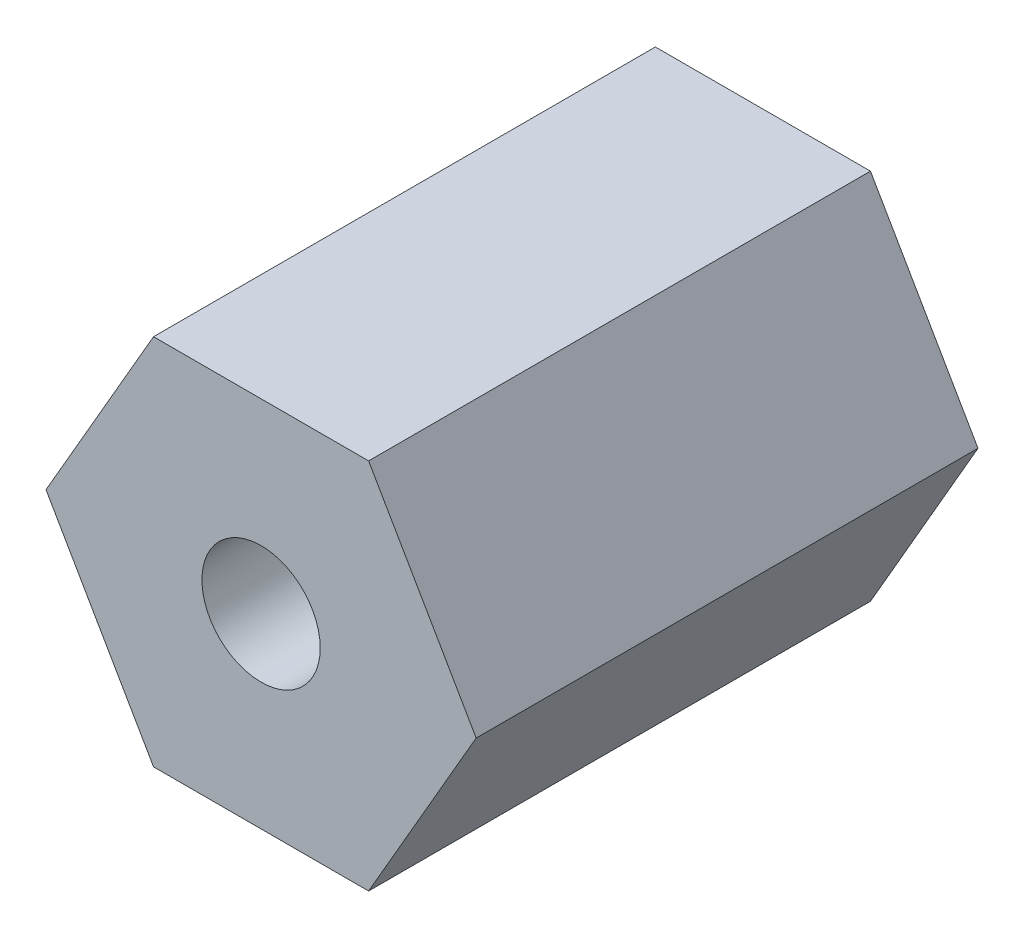
SolidWorks part; units mm, degrees
material "1060 合金"
ref_plane "前视基准面" through (0, 0, 0) normal (0, 0, 1) x (1, 0, 0)
ref_plane "上视基准面" through (0, 0, 0) normal (0, 1, 0) x (1, 0, 0)
ref_plane "右视基准面" through (0, 0, 0) normal (1, 0, 0) x (0, 0, -1)
other "Configuration Table"
sketch "草图1" plane through (0, 0, 0) normal (0, 0, 1) x (1, 0, 0)
  line L1 (-3, 5.1962) -> (-6, 0)
  line L2 (-6, 0) -> (-3, -5.1962)
  line L3 (-3, -5.1962) -> (3, -5.1962)
  line L4 (3, -5.1962) -> (6, 0)
  line L5 (6, 0) -> (3, 5.1962)
  line L6 (3, 5.1962) -> (-3, 5.1962)
  circle A0 centre (0, 0) radius 5.1962 construction
  dimension "D1" = 6
extrude "凸台-拉伸1" add sketch "草图1" along normal blind 14
hole_wizard "M4 螺纹孔2" positions "草图2" profile "草图3" tap size "M4" standard "ISO"
sketch "草图2" plane through (0, 0, 14) normal (0, 0, 1) x (1, 0, 0)
  point P0 (0, 0)
cosmetic thread "孔螺蚊线1" parameters "D1"=20, "D2"=4
sketch "草图3" plane through (0, 0, 14) normal (1, 0, 0) x (0, -1, 0)
  line L0 (0, 0) -> (0, 23.0914)
  line L1 (0, 23.0914) -> (1.65, 22.1)
  line L2 (1.65, 22.1) -> (1.65, 0)
  line L5 (1.65, 0) -> (0, 0)
  line L10 (0, 23.0914) -> (-1.65, 22.1) construction
  line L11 (0, -6.35) -> (0, 107.95) construction
  dimension "螺纹孔钻头直径" = 3.3
  dimension "螺纹孔钻头深度" = 22.1
  dimension "导头角度" = 118
